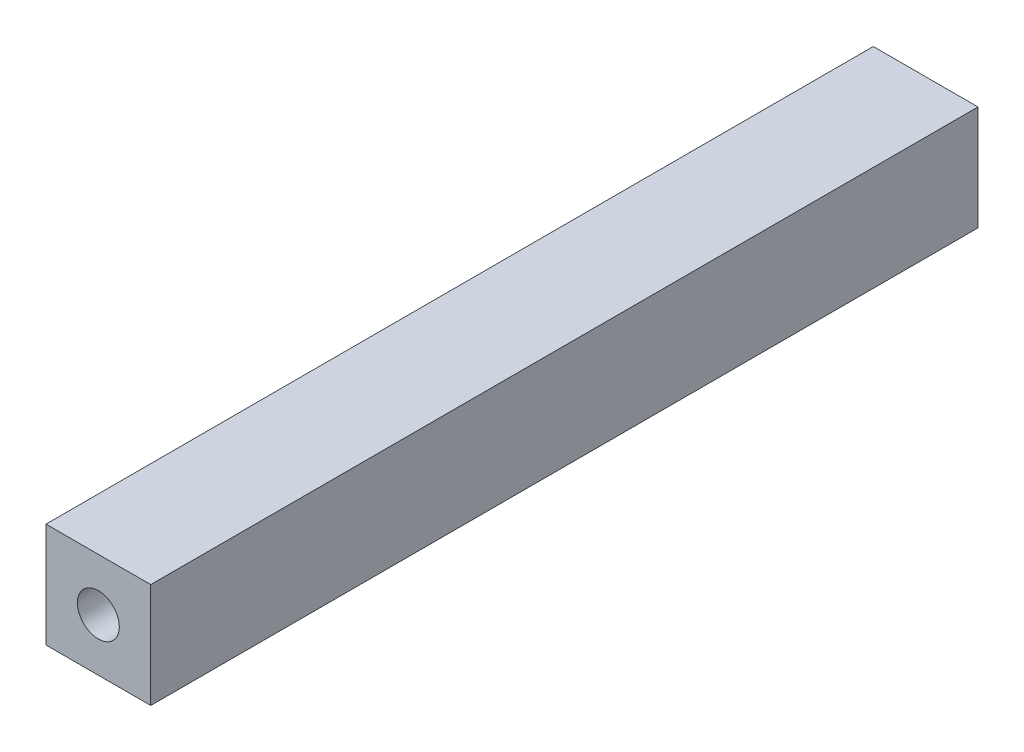
SolidWorks part; units mm, degrees
ref_plane "Front Plane" through (0, 0, 0) normal (0, 0, 1) x (1, 0, 0)
ref_plane "Top Plane" through (0, 0, 0) normal (0, 1, 0) x (1, 0, 0)
ref_plane "Right Plane" through (0, 0, 0) normal (1, 0, 0) x (0, 0, -1)
sketch "Sketch1" plane through (0, 0, 0) normal (0, 0, 1) x (1, 0, 0)
  line L1 (-5, -5) -> (5, -5)
  line L2 (-5, -5) -> (-5, 5)
  line L3 (-5, 5) -> (5, 5)
  line L4 (5, -5) -> (5, 5)
  line L5 (-5, -5) -> (5, 5) construction
  line L6 (-5, 5) -> (5, -5) construction
  circle A0 centre (0, 0) radius 2
  point P0 (0, 0)
  dimension "D2" = 4
  dimension "D1" = 10
extrude "Boss-Extrude1" add sketch "Sketch1" along normal blind 79
